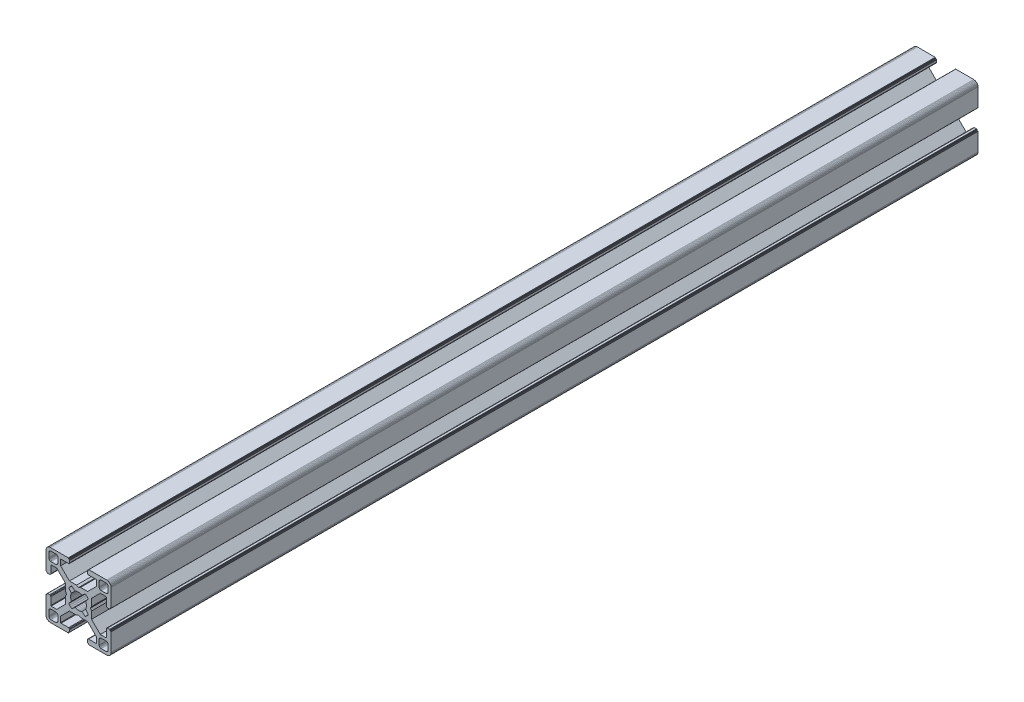
SolidWorks part; units mm, degrees
ref_plane "Front Plane" through (0, 0, 0) normal (0, 0, 1) x (1, 0, 0)
ref_plane "Top Plane" through (0, 0, 0) normal (0, 1, 0) x (1, 0, 0)
ref_plane "Right Plane" through (0, 0, 0) normal (1, 0, 0) x (0, 0, -1)
ref_plane "Plane1" through (0, 0, 0) normal (0, 0, 1) x (1, 0, 0)
sketch "Sketch1" plane through (0, 0, 0) normal (0, 0, 1) x (1, 0, 0)
  line L0 (28.3473, 29.9696) -> (28, 30)
  line L1 (28, 30) -> (19.75, 30)
  line L2 (19.75, 30) -> (19.7153, 29.997)
  line L3 (19.7153, 29.997) -> (19.6816, 29.9879)
  line L4 (19.6816, 29.9879) -> (19.65, 29.9732)
  line L5 (19.65, 29.9732) -> (19.6214, 29.9532)
  line L6 (19.6214, 29.9532) -> (19.5968, 29.9286)
  line L7 (19.5968, 29.9286) -> (19.5768, 29.9)
  line L8 (19.5768, 29.9) -> (19.5621, 29.8684)
  line L9 (19.5621, 29.8684) -> (19.553, 29.8347)
  line L10 (19.553, 29.8347) -> (19.55, 29.8)
  line L11 (19.55, 29.8) -> (19.55, 29.7)
  line L12 (19.55, 29.7) -> (19.547, 29.6653)
  line L13 (19.547, 29.6653) -> (19.5379, 29.6316)
  line L14 (19.5379, 29.6316) -> (19.5232, 29.6)
  line L15 (19.5232, 29.6) -> (19.5032, 29.5714)
  line L16 (19.5032, 29.5714) -> (19.4786, 29.5468)
  line L17 (19.4786, 29.5468) -> (19.45, 29.5268)
  line L18 (19.45, 29.5268) -> (19.4184, 29.5121)
  line L19 (19.4184, 29.5121) -> (19.3847, 29.503)
  line L20 (19.3847, 29.503) -> (19.35, 29.5)
  line L21 (19.35, 29.5) -> (19.25, 29.5)
  line L22 (19.25, 29.5) -> (19.2153, 29.497)
  line L23 (19.2153, 29.497) -> (19.1816, 29.4879)
  line L24 (19.1816, 29.4879) -> (19.15, 29.4732)
  line L25 (19.15, 29.4732) -> (19.1214, 29.4532)
  line L26 (19.1214, 29.4532) -> (19.0968, 29.4286)
  line L27 (19.0968, 29.4286) -> (19.0768, 29.4)
  line L28 (19.0768, 29.4) -> (19.0621, 29.3684)
  line L29 (19.0621, 29.3684) -> (19.053, 29.3347)
  line L30 (19.053, 29.3347) -> (19.05, 29.3)
  line L31 (19.05, 29.3) -> (19.05, 28.4)
  line L32 (19.05, 28.4) -> (19.0591, 28.2958)
  line L33 (19.0591, 28.2958) -> (19.0862, 28.1948)
  line L34 (19.0862, 28.1948) -> (19.1304, 28.1)
  line L35 (19.1304, 28.1) -> (19.1904, 28.0143)
  line L36 (19.1904, 28.0143) -> (19.2643, 27.9404)
  line L37 (19.2643, 27.9404) -> (19.35, 27.8804)
  line L38 (19.35, 27.8804) -> (19.4448, 27.8362)
  line L39 (19.4448, 27.8362) -> (19.5458, 27.8091)
  line L40 (19.5458, 27.8091) -> (19.65, 27.8)
  line L41 (19.65, 27.8) -> (23.05, 27.8)
  line L42 (23.05, 27.8) -> (23.0847, 27.7969)
  line L43 (23.0847, 27.7969) -> (23.1184, 27.7879)
  line L44 (23.1184, 27.7879) -> (23.15, 27.7732)
  line L45 (23.15, 27.7732) -> (23.1786, 27.7532)
  line L46 (23.1786, 27.7532) -> (23.2032, 27.7285)
  line L47 (23.2032, 27.7285) -> (23.2232, 27.7)
  line L48 (23.2232, 27.7) -> (23.2379, 27.6684)
  line L49 (23.2379, 27.6684) -> (23.247, 27.6347)
  line L50 (23.247, 27.6347) -> (23.25, 27.6)
  line L51 (23.25, 27.6) -> (23.25, 25.05)
  line L52 (23.25, 25.05) -> (19.2045, 21)
  line L53 (19.2045, 21) -> (15.9, 21)
  line L54 (15.9, 21) -> (15, 20.4848)
  line L55 (15, 20.4848) -> (14.1, 21)
  line L56 (14.1, 21) -> (10.7955, 21)
  line L57 (10.7955, 21) -> (7.9973, 23.8013)
  line L58 (7.9973, 23.8013) -> (6.75, 25.05)
  line L59 (6.75, 25.05) -> (6.75, 27.6)
  line L60 (6.75, 27.6) -> (6.753, 27.6347)
  line L61 (6.753, 27.6347) -> (6.7621, 27.6684)
  line L62 (6.7621, 27.6684) -> (6.7768, 27.7)
  line L63 (6.7768, 27.7) -> (6.7968, 27.7285)
  line L64 (6.7968, 27.7285) -> (6.8215, 27.7532)
  line L65 (6.8215, 27.7532) -> (6.85, 27.7732)
  line L66 (6.85, 27.7732) -> (6.8816, 27.7879)
  line L67 (6.8816, 27.7879) -> (6.9153, 27.7969)
  line L68 (6.9153, 27.7969) -> (6.95, 27.8)
  line L69 (6.95, 27.8) -> (10.35, 27.8)
  line L70 (10.35, 27.8) -> (10.4542, 27.8091)
  line L71 (10.4542, 27.8091) -> (10.5552, 27.8362)
  line L72 (10.5552, 27.8362) -> (10.65, 27.8804)
  line L73 (10.65, 27.8804) -> (10.7357, 27.9404)
  line L74 (10.7357, 27.9404) -> (10.8096, 28.0143)
  line L75 (10.8096, 28.0143) -> (10.8696, 28.1)
  line L76 (10.8696, 28.1) -> (10.9138, 28.1948)
  line L77 (10.9138, 28.1948) -> (10.9409, 28.2958)
  line L78 (10.9409, 28.2958) -> (10.95, 28.4)
  line L79 (10.95, 28.4) -> (10.95, 29.3)
  line L80 (10.95, 29.3) -> (10.947, 29.3347)
  line L81 (10.947, 29.3347) -> (10.938, 29.3684)
  line L82 (10.938, 29.3684) -> (10.9232, 29.4)
  line L83 (10.9232, 29.4) -> (10.9032, 29.4286)
  line L84 (10.9032, 29.4286) -> (10.8786, 29.4532)
  line L85 (10.8786, 29.4532) -> (10.85, 29.4732)
  line L86 (10.85, 29.4732) -> (10.8184, 29.4879)
  line L87 (10.8184, 29.4879) -> (10.7847, 29.497)
  line L88 (10.7847, 29.497) -> (10.75, 29.5)
  line L89 (10.75, 29.5) -> (10.65, 29.5)
  line L90 (10.65, 29.5) -> (10.6153, 29.503)
  line L91 (10.6153, 29.503) -> (10.5816, 29.5121)
  line L92 (10.5816, 29.5121) -> (10.55, 29.5268)
  line L93 (10.55, 29.5268) -> (10.5214, 29.5468)
  line L94 (10.5214, 29.5468) -> (10.4968, 29.5714)
  line L95 (10.4968, 29.5714) -> (10.4768, 29.6)
  line L96 (10.4768, 29.6) -> (10.4621, 29.6316)
  line L97 (10.4621, 29.6316) -> (10.453, 29.6653)
  line L98 (10.453, 29.6653) -> (10.45, 29.7)
  line L99 (10.45, 29.7) -> (10.45, 29.8)
  line L100 (10.45, 29.8) -> (10.447, 29.8347)
  line L101 (10.447, 29.8347) -> (10.4379, 29.8684)
  line L102 (10.4379, 29.8684) -> (10.4232, 29.9)
  line L103 (10.4232, 29.9) -> (10.4032, 29.9286)
  line L104 (10.4032, 29.9286) -> (10.3786, 29.9532)
  line L105 (10.3786, 29.9532) -> (10.35, 29.9732)
  line L106 (10.35, 29.9732) -> (10.3184, 29.9879)
  line L107 (10.3184, 29.9879) -> (10.2847, 29.997)
  line L108 (10.2847, 29.997) -> (10.25, 30)
  line L109 (10.25, 30) -> (2, 30)
  line L110 (2, 30) -> (1.6527, 29.9696)
  line L111 (1.6527, 29.9696) -> (1.316, 29.8794)
  line L112 (1.316, 29.8794) -> (1, 29.7321)
  line L113 (1, 29.7321) -> (0.7144, 29.5321)
  line L114 (0.7144, 29.5321) -> (0.4679, 29.2856)
  line L115 (0.4679, 29.2856) -> (0.2679, 29)
  line L116 (0.2679, 29) -> (0.1206, 28.684)
  line L117 (0.1206, 28.684) -> (0.0304, 28.3473)
  line L118 (0.0304, 28.3473) -> (0, 28)
  line L119 (0, 28) -> (0, 19.75)
  line L120 (0, 19.75) -> (0.003, 19.7153)
  line L121 (0.003, 19.7153) -> (0.0121, 19.6816)
  line L122 (0.0121, 19.6816) -> (0.0268, 19.65)
  line L123 (0.0268, 19.65) -> (0.0468, 19.6214)
  line L124 (0.0468, 19.6214) -> (0.0714, 19.5968)
  line L125 (0.0714, 19.5968) -> (0.1, 19.5768)
  line L126 (0.1, 19.5768) -> (0.1316, 19.5621)
  line L127 (0.1316, 19.5621) -> (0.1653, 19.553)
  line L128 (0.1653, 19.553) -> (0.2, 19.55)
  line L129 (0.2, 19.55) -> (0.3, 19.55)
  line L130 (0.3, 19.55) -> (0.3347, 19.547)
  line L131 (0.3347, 19.547) -> (0.3684, 19.5379)
  line L132 (0.3684, 19.5379) -> (0.4, 19.5232)
  line L133 (0.4, 19.5232) -> (0.4286, 19.5032)
  line L134 (0.4286, 19.5032) -> (0.4532, 19.4786)
  line L135 (0.4532, 19.4786) -> (0.4732, 19.45)
  line L136 (0.4732, 19.45) -> (0.4879, 19.4184)
  line L137 (0.4879, 19.4184) -> (0.497, 19.3847)
  line L138 (0.497, 19.3847) -> (0.5, 19.35)
  line L139 (0.5, 19.35) -> (0.5, 19.25)
  line L140 (0.5, 19.25) -> (0.503, 19.2153)
  line L141 (0.503, 19.2153) -> (0.5121, 19.1816)
  line L142 (0.5121, 19.1816) -> (0.5268, 19.15)
  line L143 (0.5268, 19.15) -> (0.5468, 19.1214)
  line L144 (0.5468, 19.1214) -> (0.5714, 19.0968)
  line L145 (0.5714, 19.0968) -> (0.6, 19.0768)
  line L146 (0.6, 19.0768) -> (0.6316, 19.0621)
  line L147 (0.6316, 19.0621) -> (0.6653, 19.053)
  line L148 (0.6653, 19.053) -> (0.7, 19.05)
  line L149 (0.7, 19.05) -> (1.6, 19.05)
  line L150 (1.6, 19.05) -> (1.7042, 19.0591)
  line L151 (1.7042, 19.0591) -> (1.8052, 19.0862)
  line L152 (1.8052, 19.0862) -> (1.9, 19.1304)
  line L153 (1.9, 19.1304) -> (1.9857, 19.1904)
  line L154 (1.9857, 19.1904) -> (2.0596, 19.2643)
  line L155 (2.0596, 19.2643) -> (2.1196, 19.35)
  line L156 (2.1196, 19.35) -> (2.1638, 19.4448)
  line L157 (2.1638, 19.4448) -> (2.1909, 19.5458)
  line L158 (2.1909, 19.5458) -> (2.2, 19.65)
  line L159 (2.2, 19.65) -> (2.2, 23.05)
  line L160 (2.2, 23.05) -> (2.203, 23.0847)
  line L161 (2.203, 23.0847) -> (2.2121, 23.1184)
  line L162 (2.2121, 23.1184) -> (2.2268, 23.15)
  line L163 (2.2268, 23.15) -> (2.2468, 23.1786)
  line L164 (2.2468, 23.1786) -> (2.2714, 23.2032)
  line L165 (2.2714, 23.2032) -> (2.3, 23.2232)
  line L166 (2.3, 23.2232) -> (2.3316, 23.2379)
  line L167 (2.3316, 23.2379) -> (2.3653, 23.247)
  line L168 (2.3653, 23.247) -> (2.4, 23.25)
  line L169 (2.4, 23.25) -> (4.95, 23.25)
  line L170 (4.95, 23.25) -> (7.9973, 20.2027)
  line L171 (7.9973, 20.2027) -> (8.9955, 19.2045)
  line L172 (8.9955, 19.2045) -> (8.9955, 15.9)
  line L173 (8.9955, 15.9) -> (9.5151, 15)
  line L174 (9.5151, 15) -> (8.9955, 14.1)
  line L175 (8.9955, 14.1) -> (8.9955, 10.7955)
  line L176 (8.9955, 10.7955) -> (4.95, 6.75)
  line L177 (4.95, 6.75) -> (2.4, 6.75)
  line L178 (2.4, 6.75) -> (2.3653, 6.753)
  line L179 (2.3653, 6.753) -> (2.3316, 6.7621)
  line L180 (2.3316, 6.7621) -> (2.3, 6.7768)
  line L181 (2.3, 6.7768) -> (2.2714, 6.7968)
  line L182 (2.2714, 6.7968) -> (2.2468, 6.8214)
  line L183 (2.2468, 6.8214) -> (2.2268, 6.85)
  line L184 (2.2268, 6.85) -> (2.2121, 6.8816)
  line L185 (2.2121, 6.8816) -> (2.203, 6.9153)
  line L186 (2.203, 6.9153) -> (2.2, 6.95)
  line L187 (2.2, 6.95) -> (2.2, 10.35)
  line L188 (2.2, 10.35) -> (2.1909, 10.4542)
  line L189 (2.1909, 10.4542) -> (2.1638, 10.5552)
  line L190 (2.1638, 10.5552) -> (2.1196, 10.65)
  line L191 (2.1196, 10.65) -> (2.0596, 10.7357)
  line L192 (2.0596, 10.7357) -> (1.9857, 10.8096)
  line L193 (1.9857, 10.8096) -> (1.9, 10.8696)
  line L194 (1.9, 10.8696) -> (1.8052, 10.9138)
  line L195 (1.8052, 10.9138) -> (1.7042, 10.9409)
  line L196 (1.7042, 10.9409) -> (1.6, 10.95)
  line L197 (1.6, 10.95) -> (0.7, 10.95)
  line L198 (0.7, 10.95) -> (0.6653, 10.9469)
  line L199 (0.6653, 10.9469) -> (0.6316, 10.9379)
  line L200 (0.6316, 10.9379) -> (0.6, 10.9232)
  line L201 (0.6, 10.9232) -> (0.5715, 10.9032)
  line L202 (0.5715, 10.9032) -> (0.5468, 10.8785)
  line L203 (0.5468, 10.8785) -> (0.5268, 10.85)
  line L204 (0.5268, 10.85) -> (0.5121, 10.8184)
  line L205 (0.5121, 10.8184) -> (0.503, 10.7847)
  line L206 (0.503, 10.7847) -> (0.5, 10.75)
  line L207 (0.5, 10.75) -> (0.5, 10.65)
  line L208 (0.5, 10.65) -> (0.497, 10.6153)
  line L209 (0.497, 10.6153) -> (0.4879, 10.5816)
  line L210 (0.4879, 10.5816) -> (0.4732, 10.55)
  line L211 (0.4732, 10.55) -> (0.4532, 10.5214)
  line L212 (0.4532, 10.5214) -> (0.4286, 10.4968)
  line L213 (0.4286, 10.4968) -> (0.4, 10.4768)
  line L214 (0.4, 10.4768) -> (0.3684, 10.4621)
  line L215 (0.3684, 10.4621) -> (0.3347, 10.453)
  line L216 (0.3347, 10.453) -> (0.3, 10.45)
  line L217 (0.3, 10.45) -> (0.2, 10.45)
  line L218 (0.2, 10.45) -> (0.1653, 10.447)
  line L219 (0.1653, 10.447) -> (0.1316, 10.4379)
  line L220 (0.1316, 10.4379) -> (0.1, 10.4232)
  line L221 (0.1, 10.4232) -> (0.0714, 10.4032)
  line L222 (0.0714, 10.4032) -> (0.0468, 10.3786)
  line L223 (0.0468, 10.3786) -> (0.0268, 10.35)
  line L224 (0.0268, 10.35) -> (0.0121, 10.3184)
  line L225 (0.0121, 10.3184) -> (0.003, 10.2847)
  line L226 (0.003, 10.2847) -> (0, 10.25)
  line L227 (0, 10.25) -> (0, 2)
  line L228 (0, 2) -> (0.0304, 1.6527)
  line L229 (0.0304, 1.6527) -> (0.1206, 1.316)
  line L230 (0.1206, 1.316) -> (0.2679, 1)
  line L231 (0.2679, 1) -> (0.4679, 0.7144)
  line L232 (0.4679, 0.7144) -> (0.7144, 0.4679)
  line L233 (0.7144, 0.4679) -> (1, 0.2679)
  line L234 (1, 0.2679) -> (1.316, 0.1206)
  line L235 (1.316, 0.1206) -> (1.6527, 0.0304)
  line L236 (1.6527, 0.0304) -> (2, 0)
  line L237 (2, 0) -> (10.25, 0)
  line L238 (10.25, 0) -> (10.2847, 0.003)
  line L239 (10.2847, 0.003) -> (10.3184, 0.0121)
  line L240 (10.3184, 0.0121) -> (10.35, 0.0268)
  line L241 (10.35, 0.0268) -> (10.3786, 0.0468)
  line L242 (10.3786, 0.0468) -> (10.4032, 0.0714)
  line L243 (10.4032, 0.0714) -> (10.4232, 0.1)
  line L244 (10.4232, 0.1) -> (10.4379, 0.1316)
  line L245 (10.4379, 0.1316) -> (10.447, 0.1653)
  line L246 (10.447, 0.1653) -> (10.45, 0.2)
  line L247 (10.45, 0.2) -> (10.45, 0.3)
  line L248 (10.45, 0.3) -> (10.453, 0.3347)
  line L249 (10.453, 0.3347) -> (10.4621, 0.3684)
  line L250 (10.4621, 0.3684) -> (10.4768, 0.4)
  line L251 (10.4768, 0.4) -> (10.4968, 0.4286)
  line L252 (10.4968, 0.4286) -> (10.5214, 0.4532)
  line L253 (10.5214, 0.4532) -> (10.55, 0.4732)
  line L254 (10.55, 0.4732) -> (10.5816, 0.4879)
  line L255 (10.5816, 0.4879) -> (10.6153, 0.497)
  line L256 (10.6153, 0.497) -> (10.65, 0.5)
  line L257 (10.65, 0.5) -> (10.75, 0.5)
  line L258 (10.75, 0.5) -> (10.7847, 0.503)
  line L259 (10.7847, 0.503) -> (10.8184, 0.5121)
  line L260 (10.8184, 0.5121) -> (10.85, 0.5268)
  line L261 (10.85, 0.5268) -> (10.8785, 0.5468)
  line L262 (10.8785, 0.5468) -> (10.9032, 0.5715)
  line L263 (10.9032, 0.5715) -> (10.9232, 0.6)
  line L264 (10.9232, 0.6) -> (10.9379, 0.6316)
  line L265 (10.9379, 0.6316) -> (10.9469, 0.6653)
  line L266 (10.9469, 0.6653) -> (10.95, 0.7)
  line L267 (10.95, 0.7) -> (10.95, 1.6)
  line L268 (10.95, 1.6) -> (10.9409, 1.7042)
  line L269 (10.9409, 1.7042) -> (10.9138, 1.8052)
  line L270 (10.9138, 1.8052) -> (10.8696, 1.9)
  line L271 (10.8696, 1.9) -> (10.8096, 1.9857)
  line L272 (10.8096, 1.9857) -> (10.7357, 2.0596)
  line L273 (10.7357, 2.0596) -> (10.65, 2.1196)
  line L274 (10.65, 2.1196) -> (10.5552, 2.1638)
  line L275 (10.5552, 2.1638) -> (10.4542, 2.1909)
  line L276 (10.4542, 2.1909) -> (10.35, 2.2)
  line L277 (10.35, 2.2) -> (6.95, 2.2)
  line L278 (6.95, 2.2) -> (6.9153, 2.203)
  line L279 (6.9153, 2.203) -> (6.8816, 2.212)
  line L280 (6.8816, 2.212) -> (6.85, 2.2268)
  line L281 (6.85, 2.2268) -> (6.8215, 2.2468)
  line L282 (6.8215, 2.2468) -> (6.7968, 2.2714)
  line L283 (6.7968, 2.2714) -> (6.7768, 2.3)
  line L284 (6.7768, 2.3) -> (6.7621, 2.3316)
  line L285 (6.7621, 2.3316) -> (6.753, 2.3653)
  line L286 (6.753, 2.3653) -> (6.75, 2.4)
  line L287 (6.75, 2.4) -> (6.75, 4.95)
  line L288 (6.75, 4.95) -> (9.7875, 7.9908)
  line L289 (9.7875, 7.9908) -> (10.7955, 9)
  line L290 (10.7955, 9) -> (14.1, 9)
  line L291 (14.1, 9) -> (15, 9.5151)
  line L292 (15, 9.5151) -> (15.9, 9)
  line L293 (15.9, 9) -> (19.2045, 9)
  line L294 (19.2045, 9) -> (20.2126, 7.9908)
  line L295 (20.2126, 7.9908) -> (23.25, 4.95)
  line L296 (23.25, 4.95) -> (23.25, 2.4)
  line L297 (23.25, 2.4) -> (23.247, 2.3653)
  line L298 (23.247, 2.3653) -> (23.2379, 2.3316)
  line L299 (23.2379, 2.3316) -> (23.2232, 2.3)
  line L300 (23.2232, 2.3) -> (23.2032, 2.2714)
  line L301 (23.2032, 2.2714) -> (23.1786, 2.2468)
  line L302 (23.1786, 2.2468) -> (23.15, 2.2268)
  line L303 (23.15, 2.2268) -> (23.1184, 2.212)
  line L304 (23.1184, 2.212) -> (23.0847, 2.203)
  line L305 (23.0847, 2.203) -> (23.05, 2.2)
  line L306 (23.05, 2.2) -> (19.65, 2.2)
  line L307 (19.65, 2.2) -> (19.5458, 2.1909)
  line L308 (19.5458, 2.1909) -> (19.4448, 2.1638)
  line L309 (19.4448, 2.1638) -> (19.35, 2.1196)
  line L310 (19.35, 2.1196) -> (19.2643, 2.0596)
  line L311 (19.2643, 2.0596) -> (19.1904, 1.9857)
  line L312 (19.1904, 1.9857) -> (19.1304, 1.9)
  line L313 (19.1304, 1.9) -> (19.0862, 1.8052)
  line L314 (19.0862, 1.8052) -> (19.0591, 1.7042)
  line L315 (19.0591, 1.7042) -> (19.05, 1.6)
  line L316 (19.05, 1.6) -> (19.05, 0.7)
  line L317 (19.05, 0.7) -> (19.053, 0.6653)
  line L318 (19.053, 0.6653) -> (19.0621, 0.6316)
  line L319 (19.0621, 0.6316) -> (19.0768, 0.6)
  line L320 (19.0768, 0.6) -> (19.0968, 0.5714)
  line L321 (19.0968, 0.5714) -> (19.1214, 0.5468)
  line L322 (19.1214, 0.5468) -> (19.15, 0.5268)
  line L323 (19.15, 0.5268) -> (19.1816, 0.5121)
  line L324 (19.1816, 0.5121) -> (19.2153, 0.503)
  line L325 (19.2153, 0.503) -> (19.25, 0.5)
  line L326 (19.25, 0.5) -> (19.35, 0.5)
  line L327 (19.35, 0.5) -> (19.3847, 0.497)
  line L328 (19.3847, 0.497) -> (19.4184, 0.4879)
  line L329 (19.4184, 0.4879) -> (19.45, 0.4732)
  line L330 (19.45, 0.4732) -> (19.4786, 0.4532)
  line L331 (19.4786, 0.4532) -> (19.5032, 0.4286)
  line L332 (19.5032, 0.4286) -> (19.5232, 0.4)
  line L333 (19.5232, 0.4) -> (19.5379, 0.3684)
  line L334 (19.5379, 0.3684) -> (19.547, 0.3347)
  line L335 (19.547, 0.3347) -> (19.55, 0.3)
  line L336 (19.55, 0.3) -> (19.55, 0.2)
  line L337 (19.55, 0.2) -> (19.553, 0.1653)
  line L338 (19.553, 0.1653) -> (19.5621, 0.1316)
  line L339 (19.5621, 0.1316) -> (19.5768, 0.1)
  line L340 (19.5768, 0.1) -> (19.5968, 0.0714)
  line L341 (19.5968, 0.0714) -> (19.6214, 0.0468)
  line L342 (19.6214, 0.0468) -> (19.65, 0.0268)
  line L343 (19.65, 0.0268) -> (19.6816, 0.0121)
  line L344 (19.6816, 0.0121) -> (19.7153, 0.003)
  line L345 (19.7153, 0.003) -> (19.75, 0)
  line L346 (19.75, 0) -> (28, 0)
  line L347 (28, 0) -> (28.3473, 0.0304)
  line L348 (28.3473, 0.0304) -> (28.684, 0.1206)
  line L349 (28.684, 0.1206) -> (29, 0.2679)
  line L350 (29, 0.2679) -> (29.2856, 0.4679)
  line L351 (29.2856, 0.4679) -> (29.5321, 0.7144)
  line L352 (29.5321, 0.7144) -> (29.7321, 1)
  line L353 (29.7321, 1) -> (29.8794, 1.316)
  line L354 (29.8794, 1.316) -> (29.9696, 1.6527)
  line L355 (29.9696, 1.6527) -> (30, 2)
  line L356 (30, 2) -> (30, 10.25)
  line L357 (30, 10.25) -> (29.997, 10.2847)
  line L358 (29.997, 10.2847) -> (29.988, 10.3184)
  line L359 (29.988, 10.3184) -> (29.9732, 10.35)
  line L360 (29.9732, 10.35) -> (29.9532, 10.3785)
  line L361 (29.9532, 10.3785) -> (29.9286, 10.4032)
  line L362 (29.9286, 10.4032) -> (29.9, 10.4232)
  line L363 (29.9, 10.4232) -> (29.8684, 10.4379)
  line L364 (29.8684, 10.4379) -> (29.8347, 10.447)
  line L365 (29.8347, 10.447) -> (29.8, 10.45)
  line L366 (29.8, 10.45) -> (29.7, 10.45)
  line L367 (29.7, 10.45) -> (29.6649, 10.4534)
  line L368 (29.6649, 10.4534) -> (29.6312, 10.4624)
  line L369 (29.6312, 10.4624) -> (29.5996, 10.4772)
  line L370 (29.5996, 10.4772) -> (29.5711, 10.4972)
  line L371 (29.5711, 10.4972) -> (29.5464, 10.5218)
  line L372 (29.5464, 10.5218) -> (29.5264, 10.5504)
  line L373 (29.5264, 10.5504) -> (29.5117, 10.582)
  line L374 (29.5117, 10.582) -> (29.5027, 10.6156)
  line L375 (29.5027, 10.6156) -> (29.4996, 10.6504)
  line L376 (29.4996, 10.6504) -> (29.4996, 10.7504)
  line L377 (29.4996, 10.7504) -> (29.497, 10.7847)
  line L378 (29.497, 10.7847) -> (29.4879, 10.8184)
  line L379 (29.4879, 10.8184) -> (29.4732, 10.85)
  line L380 (29.4732, 10.85) -> (29.4532, 10.8785)
  line L381 (29.4532, 10.8785) -> (29.4286, 10.9032)
  line L382 (29.4286, 10.9032) -> (29.4, 10.9232)
  line L383 (29.4, 10.9232) -> (29.3684, 10.9379)
  line L384 (29.3684, 10.9379) -> (29.3347, 10.9469)
  line L385 (29.3347, 10.9469) -> (29.3, 10.95)
  line L386 (29.3, 10.95) -> (28.4, 10.95)
  line L387 (28.4, 10.95) -> (28.2958, 10.9409)
  line L388 (28.2958, 10.9409) -> (28.1948, 10.9138)
  line L389 (28.1948, 10.9138) -> (28.1, 10.8696)
  line L390 (28.1, 10.8696) -> (28.0143, 10.8096)
  line L391 (28.0143, 10.8096) -> (27.9404, 10.7357)
  line L392 (27.9404, 10.7357) -> (27.8804, 10.65)
  line L393 (27.8804, 10.65) -> (27.8362, 10.5552)
  line L394 (27.8362, 10.5552) -> (27.8091, 10.4542)
  line L395 (27.8091, 10.4542) -> (27.8, 10.35)
  line L396 (27.8, 10.35) -> (27.8, 6.95)
  line L397 (27.8, 6.95) -> (27.797, 6.9153)
  line L398 (27.797, 6.9153) -> (27.7879, 6.8816)
  line L399 (27.7879, 6.8816) -> (27.7732, 6.85)
  line L400 (27.7732, 6.85) -> (27.7532, 6.8214)
  line L401 (27.7532, 6.8214) -> (27.7286, 6.7968)
  line L402 (27.7286, 6.7968) -> (27.7, 6.7768)
  line L403 (27.7, 6.7768) -> (27.6684, 6.7621)
  line L404 (27.6684, 6.7621) -> (27.6347, 6.753)
  line L405 (27.6347, 6.753) -> (27.6, 6.75)
  line L406 (27.6, 6.75) -> (25.05, 6.75)
  line L407 (25.05, 6.75) -> (23.8092, 7.9908)
  line L408 (23.8092, 7.9908) -> (21.0045, 10.7955)
  line L409 (21.0045, 10.7955) -> (21.0045, 14.1)
  line L410 (21.0045, 14.1) -> (20.4849, 15)
  line L411 (20.4849, 15) -> (21.0045, 15.9)
  line L412 (21.0045, 15.9) -> (21.0045, 19.2045)
  line L413 (21.0045, 19.2045) -> (25.05, 23.25)
  line L414 (25.05, 23.25) -> (27.6, 23.25)
  line L415 (27.6, 23.25) -> (27.6347, 23.247)
  line L416 (27.6347, 23.247) -> (27.6684, 23.2379)
  line L417 (27.6684, 23.2379) -> (27.7, 23.2232)
  line L418 (27.7, 23.2232) -> (27.7286, 23.2032)
  line L419 (27.7286, 23.2032) -> (27.7532, 23.1786)
  line L420 (27.7532, 23.1786) -> (27.7732, 23.15)
  line L421 (27.7732, 23.15) -> (27.7879, 23.1184)
  line L422 (27.7879, 23.1184) -> (27.797, 23.0847)
  line L423 (27.797, 23.0847) -> (27.8, 23.05)
  line L424 (27.8, 23.05) -> (27.8, 19.65)
  line L425 (27.8, 19.65) -> (27.8091, 19.5458)
  line L426 (27.8091, 19.5458) -> (27.8362, 19.4448)
  line L427 (27.8362, 19.4448) -> (27.8804, 19.35)
  line L428 (27.8804, 19.35) -> (27.9404, 19.2643)
  line L429 (27.9404, 19.2643) -> (28.0143, 19.1904)
  line L430 (28.0143, 19.1904) -> (28.1, 19.1304)
  line L431 (28.1, 19.1304) -> (28.1948, 19.0862)
  line L432 (28.1948, 19.0862) -> (28.2958, 19.0591)
  line L433 (28.2958, 19.0591) -> (28.4, 19.05)
  line L434 (28.4, 19.05) -> (29.3, 19.05)
  line L435 (29.3, 19.05) -> (29.3347, 19.053)
  line L436 (29.3347, 19.053) -> (29.3684, 19.0621)
  line L437 (29.3684, 19.0621) -> (29.4, 19.0768)
  line L438 (29.4, 19.0768) -> (29.4282, 19.0971)
  line L439 (29.4282, 19.0971) -> (29.4528, 19.1218)
  line L440 (29.4528, 19.1218) -> (29.4728, 19.1504)
  line L441 (29.4728, 19.1504) -> (29.4876, 19.182)
  line L442 (29.4876, 19.182) -> (29.4966, 19.2156)
  line L443 (29.4966, 19.2156) -> (29.4996, 19.2504)
  line L444 (29.4996, 19.2504) -> (29.4996, 19.3504)
  line L445 (29.4996, 19.3504) -> (29.5027, 19.3851)
  line L446 (29.5027, 19.3851) -> (29.5117, 19.4188)
  line L447 (29.5117, 19.4188) -> (29.5264, 19.4504)
  line L448 (29.5264, 19.4504) -> (29.5464, 19.4789)
  line L449 (29.5464, 19.4789) -> (29.5711, 19.5036)
  line L450 (29.5711, 19.5036) -> (29.5996, 19.5236)
  line L451 (29.5996, 19.5236) -> (29.6312, 19.5383)
  line L452 (29.6312, 19.5383) -> (29.6649, 19.5473)
  line L453 (29.6649, 19.5473) -> (29.7, 19.55)
  line L454 (29.7, 19.55) -> (29.8, 19.55)
  line L455 (29.8, 19.55) -> (29.8347, 19.553)
  line L456 (29.8347, 19.553) -> (29.8684, 19.5621)
  line L457 (29.8684, 19.5621) -> (29.9, 19.5768)
  line L458 (29.9, 19.5768) -> (29.9286, 19.5968)
  line L459 (29.9286, 19.5968) -> (29.9532, 19.6214)
  line L460 (29.9532, 19.6214) -> (29.9732, 19.65)
  line L461 (29.9732, 19.65) -> (29.9879, 19.6816)
  line L462 (29.9879, 19.6816) -> (29.997, 19.7153)
  line L463 (29.997, 19.7153) -> (30, 19.75)
  line L464 (30, 19.75) -> (30, 28)
  line L465 (30, 28) -> (29.9696, 28.3473)
  line L466 (29.9696, 28.3473) -> (29.8794, 28.684)
  line L467 (29.8794, 28.684) -> (29.7321, 29)
  line L468 (29.7321, 29) -> (29.5321, 29.2856)
  line L469 (29.5321, 29.2856) -> (29.2856, 29.5321)
  line L470 (29.2856, 29.5321) -> (29, 29.7321)
  line L471 (29, 29.7321) -> (28.684, 29.8794)
  line L472 (28.684, 29.8794) -> (28.3473, 29.9696)
  line L473 (1.3, 25.5) -> (1.3, 27.7)
  line L474 (1.3, 27.7) -> (1.3123, 27.8564)
  line L475 (1.3123, 27.8564) -> (1.3489, 28.009)
  line L476 (1.3489, 28.009) -> (1.409, 28.154)
  line L477 (1.409, 28.154) -> (1.491, 28.2878)
  line L478 (1.491, 28.2878) -> (1.5929, 28.4071)
  line L479 (1.5929, 28.4071) -> (1.7122, 28.509)
  line L480 (1.7122, 28.509) -> (1.846, 28.591)
  line L481 (1.846, 28.591) -> (1.991, 28.6511)
  line L482 (1.991, 28.6511) -> (2.1436, 28.6877)
  line L483 (2.1436, 28.6877) -> (2.3, 28.7)
  line L484 (2.3, 28.7) -> (4.5, 28.7)
  line L485 (4.5, 28.7) -> (4.6564, 28.6877)
  line L486 (4.6564, 28.6877) -> (4.809, 28.6511)
  line L487 (4.809, 28.6511) -> (4.954, 28.591)
  line L488 (4.954, 28.591) -> (5.0878, 28.509)
  line L489 (5.0878, 28.509) -> (5.2071, 28.4071)
  line L490 (5.2071, 28.4071) -> (5.309, 28.2878)
  line L491 (5.309, 28.2878) -> (5.391, 28.154)
  line L492 (5.391, 28.154) -> (5.4511, 28.009)
  line L493 (5.4511, 28.009) -> (5.4877, 27.8564)
  line L494 (5.4877, 27.8564) -> (5.5, 27.7)
  line L495 (5.5, 27.7) -> (5.5, 25.5)
  line L496 (5.5, 25.5) -> (5.4877, 25.3436)
  line L497 (5.4877, 25.3436) -> (5.4511, 25.191)
  line L498 (5.4511, 25.191) -> (5.391, 25.046)
  line L499 (5.391, 25.046) -> (5.309, 24.9122)
  line L500 (5.309, 24.9122) -> (5.2071, 24.7929)
  line L501 (5.2071, 24.7929) -> (5.0878, 24.691)
  line L502 (5.0878, 24.691) -> (4.954, 24.609)
  line L503 (4.954, 24.609) -> (4.809, 24.5489)
  line L504 (4.809, 24.5489) -> (4.6564, 24.5123)
  line L505 (4.6564, 24.5123) -> (4.5, 24.5)
  line L506 (4.5, 24.5) -> (2.3, 24.5)
  line L507 (2.3, 24.5) -> (2.1436, 24.5123)
  line L508 (2.1436, 24.5123) -> (1.991, 24.5489)
  line L509 (1.991, 24.5489) -> (1.846, 24.609)
  line L510 (1.846, 24.609) -> (1.7122, 24.691)
  line L511 (1.7122, 24.691) -> (1.5929, 24.7929)
  line L512 (1.5929, 24.7929) -> (1.491, 24.9122)
  line L513 (1.491, 24.9122) -> (1.409, 25.046)
  line L514 (1.409, 25.046) -> (1.3489, 25.191)
  line L515 (1.3489, 25.191) -> (1.3123, 25.3436)
  line L516 (1.3123, 25.3436) -> (1.3, 25.5)
  line L517 (25.3436, 28.6877) -> (25.5, 28.7)
  line L518 (25.5, 28.7) -> (27.7, 28.7)
  line L519 (27.7, 28.7) -> (27.8564, 28.6877)
  line L520 (27.8564, 28.6877) -> (28.009, 28.6511)
  line L521 (28.009, 28.6511) -> (28.154, 28.591)
  line L522 (28.154, 28.591) -> (28.2878, 28.509)
  line L523 (28.2878, 28.509) -> (28.4071, 28.4071)
  line L524 (28.4071, 28.4071) -> (28.509, 28.2878)
  line L525 (28.509, 28.2878) -> (28.591, 28.154)
  line L526 (28.591, 28.154) -> (28.6511, 28.009)
  line L527 (28.6511, 28.009) -> (28.6877, 27.8564)
  line L528 (28.6877, 27.8564) -> (28.7, 27.7)
  line L529 (28.7, 27.7) -> (28.7, 25.5)
  line L530 (28.7, 25.5) -> (28.6877, 25.3436)
  line L531 (28.6877, 25.3436) -> (28.6511, 25.191)
  line L532 (28.6511, 25.191) -> (28.591, 25.046)
  line L533 (28.591, 25.046) -> (28.509, 24.9122)
  line L534 (28.509, 24.9122) -> (28.4071, 24.7929)
  line L535 (28.4071, 24.7929) -> (28.2878, 24.691)
  line L536 (28.2878, 24.691) -> (28.154, 24.609)
  line L537 (28.154, 24.609) -> (28.009, 24.5489)
  line L538 (28.009, 24.5489) -> (27.8564, 24.5123)
  line L539 (27.8564, 24.5123) -> (27.7, 24.5)
  line L540 (27.7, 24.5) -> (25.5, 24.5)
  line L541 (25.5, 24.5) -> (25.3436, 24.5123)
  line L542 (25.3436, 24.5123) -> (25.191, 24.5489)
  line L543 (25.191, 24.5489) -> (25.046, 24.609)
  line L544 (25.046, 24.609) -> (24.9122, 24.691)
  line L545 (24.9122, 24.691) -> (24.7929, 24.7929)
  line L546 (24.7929, 24.7929) -> (24.691, 24.9122)
  line L547 (24.691, 24.9122) -> (24.609, 25.046)
  line L548 (24.609, 25.046) -> (24.5489, 25.191)
  line L549 (24.5489, 25.191) -> (24.5123, 25.3436)
  line L550 (24.5123, 25.3436) -> (24.5, 25.5)
  line L551 (24.5, 25.5) -> (24.5, 27.7)
  line L552 (24.5, 27.7) -> (24.5123, 27.8564)
  line L553 (24.5123, 27.8564) -> (24.5489, 28.009)
  line L554 (24.5489, 28.009) -> (24.609, 28.154)
  line L555 (24.609, 28.154) -> (24.691, 28.2878)
  line L556 (24.691, 28.2878) -> (24.7929, 28.4071)
  line L557 (24.7929, 28.4071) -> (24.9122, 28.509)
  line L558 (24.9122, 28.509) -> (25.046, 28.591)
  line L559 (25.046, 28.591) -> (25.191, 28.6511)
  line L560 (25.191, 28.6511) -> (25.3436, 28.6877)
  line L561 (15, 18.65) -> (15.55, 18.6083)
  line L562 (15.55, 18.6083) -> (16.0875, 18.4842)
  line L563 (16.0875, 18.4842) -> (16.6001, 18.2806)
  line L564 (16.6001, 18.2806) -> (18.1359, 19.5184)
  line L565 (18.1359, 19.5184) -> (18.645, 19.1187)
  line L566 (18.645, 19.1187) -> (19.1036, 18.6621)
  line L567 (19.1036, 18.6621) -> (19.5053, 18.1547)
  line L568 (19.5053, 18.1547) -> (18.2806, 16.6001)
  line L569 (18.2806, 16.6001) -> (18.4842, 16.0875)
  line L570 (18.4842, 16.0875) -> (18.6083, 15.55)
  line L571 (18.6083, 15.55) -> (18.65, 15)
  line L572 (18.65, 15) -> (18.6083, 14.45)
  line L573 (18.6083, 14.45) -> (18.4842, 13.9125)
  line L574 (18.4842, 13.9125) -> (18.2806, 13.3999)
  line L575 (18.2806, 13.3999) -> (19.5053, 11.8453)
  line L576 (19.5053, 11.8453) -> (19.1036, 11.3379)
  line L577 (19.1036, 11.3379) -> (18.645, 10.8813)
  line L578 (18.645, 10.8813) -> (18.1359, 10.4816)
  line L579 (18.1359, 10.4816) -> (16.6001, 11.7194)
  line L580 (16.6001, 11.7194) -> (16.0875, 11.5158)
  line L581 (16.0875, 11.5158) -> (15.55, 11.3917)
  line L582 (15.55, 11.3917) -> (15, 11.35)
  line L583 (15, 11.35) -> (14.45, 11.3917)
  line L584 (14.45, 11.3917) -> (13.9125, 11.5158)
  line L585 (13.9125, 11.5158) -> (13.3999, 11.7194)
  line L586 (13.3999, 11.7194) -> (11.8641, 10.4816)
  line L587 (11.8641, 10.4816) -> (11.355, 10.8813)
  line L588 (11.355, 10.8813) -> (10.8964, 11.3379)
  line L589 (10.8964, 11.3379) -> (10.4947, 11.8453)
  line L590 (10.4947, 11.8453) -> (11.7194, 13.3999)
  line L591 (11.7194, 13.3999) -> (11.5158, 13.9125)
  line L592 (11.5158, 13.9125) -> (11.3917, 14.45)
  line L593 (11.3917, 14.45) -> (11.35, 15)
  line L594 (11.35, 15) -> (11.3917, 15.55)
  line L595 (11.3917, 15.55) -> (11.5158, 16.0875)
  line L596 (11.5158, 16.0875) -> (11.7194, 16.6001)
  line L597 (11.7194, 16.6001) -> (10.4947, 18.1547)
  line L598 (10.4947, 18.1547) -> (10.8964, 18.6621)
  line L599 (10.8964, 18.6621) -> (11.355, 19.1187)
  line L600 (11.355, 19.1187) -> (11.8641, 19.5184)
  line L601 (11.8641, 19.5184) -> (13.3999, 18.2806)
  line L602 (13.3999, 18.2806) -> (13.9125, 18.4842)
  line L603 (13.9125, 18.4842) -> (14.45, 18.6083)
  line L604 (14.45, 18.6083) -> (15, 18.65)
  line L605 (4.5, 1.3) -> (2.3, 1.3)
  line L606 (2.3, 1.3) -> (2.1436, 1.3123)
  line L607 (2.1436, 1.3123) -> (1.991, 1.3489)
  line L608 (1.991, 1.3489) -> (1.846, 1.409)
  line L609 (1.846, 1.409) -> (1.7122, 1.491)
  line L610 (1.7122, 1.491) -> (1.5929, 1.5929)
  line L611 (1.5929, 1.5929) -> (1.491, 1.7122)
  line L612 (1.491, 1.7122) -> (1.409, 1.846)
  line L613 (1.409, 1.846) -> (1.3489, 1.991)
  line L614 (1.3489, 1.991) -> (1.3123, 2.1436)
  line L615 (1.3123, 2.1436) -> (1.3, 2.3)
  line L616 (1.3, 2.3) -> (1.3, 4.5)
  line L617 (1.3, 4.5) -> (1.3123, 4.6564)
  line L618 (1.3123, 4.6564) -> (1.3489, 4.809)
  line L619 (1.3489, 4.809) -> (1.409, 4.954)
  line L620 (1.409, 4.954) -> (1.491, 5.0878)
  line L621 (1.491, 5.0878) -> (1.5929, 5.2071)
  line L622 (1.5929, 5.2071) -> (1.7122, 5.309)
  line L623 (1.7122, 5.309) -> (1.846, 5.391)
  line L624 (1.846, 5.391) -> (1.991, 5.4511)
  line L625 (1.991, 5.4511) -> (2.1436, 5.4877)
  line L626 (2.1436, 5.4877) -> (2.3, 5.5)
  line L627 (2.3, 5.5) -> (4.5, 5.5)
  line L628 (4.5, 5.5) -> (4.6564, 5.4877)
  line L629 (4.6564, 5.4877) -> (4.809, 5.4511)
  line L630 (4.809, 5.4511) -> (4.954, 5.391)
  line L631 (4.954, 5.391) -> (5.0878, 5.309)
  line L632 (5.0878, 5.309) -> (5.2071, 5.2071)
  line L633 (5.2071, 5.2071) -> (5.309, 5.0878)
  line L634 (5.309, 5.0878) -> (5.391, 4.954)
  line L635 (5.391, 4.954) -> (5.4511, 4.809)
  line L636 (5.4511, 4.809) -> (5.4877, 4.6564)
  line L637 (5.4877, 4.6564) -> (5.5, 4.5)
  line L638 (5.5, 4.5) -> (5.5, 2.3)
  line L639 (5.5, 2.3) -> (5.4877, 2.1436)
  line L640 (5.4877, 2.1436) -> (5.4511, 1.991)
  line L641 (5.4511, 1.991) -> (5.391, 1.846)
  line L642 (5.391, 1.846) -> (5.309, 1.7122)
  line L643 (5.309, 1.7122) -> (5.2071, 1.5929)
  line L644 (5.2071, 1.5929) -> (5.0878, 1.491)
  line L645 (5.0878, 1.491) -> (4.954, 1.409)
  line L646 (4.954, 1.409) -> (4.809, 1.3489)
  line L647 (4.809, 1.3489) -> (4.6564, 1.3123)
  line L648 (4.6564, 1.3123) -> (4.5, 1.3)
  line L649 (27.7, 1.3) -> (25.5, 1.3)
  line L650 (25.5, 1.3) -> (25.3436, 1.3123)
  line L651 (25.3436, 1.3123) -> (25.191, 1.3489)
  line L652 (25.191, 1.3489) -> (25.046, 1.409)
  line L653 (25.046, 1.409) -> (24.9122, 1.491)
  line L654 (24.9122, 1.491) -> (24.7929, 1.5929)
  line L655 (24.7929, 1.5929) -> (24.691, 1.7122)
  line L656 (24.691, 1.7122) -> (24.609, 1.846)
  line L657 (24.609, 1.846) -> (24.5489, 1.991)
  line L658 (24.5489, 1.991) -> (24.5123, 2.1436)
  line L659 (24.5123, 2.1436) -> (24.5, 2.3)
  line L660 (24.5, 2.3) -> (24.5, 4.5)
  line L661 (24.5, 4.5) -> (24.5123, 4.6564)
  line L662 (24.5123, 4.6564) -> (24.5489, 4.809)
  line L663 (24.5489, 4.809) -> (24.609, 4.954)
  line L664 (24.609, 4.954) -> (24.691, 5.0878)
  line L665 (24.691, 5.0878) -> (24.7929, 5.2071)
  line L666 (24.7929, 5.2071) -> (24.9122, 5.309)
  line L667 (24.9122, 5.309) -> (25.046, 5.391)
  line L668 (25.046, 5.391) -> (25.191, 5.4511)
  line L669 (25.191, 5.4511) -> (25.3436, 5.4877)
  line L670 (25.3436, 5.4877) -> (25.5, 5.5)
  line L671 (25.5, 5.5) -> (27.7, 5.5)
  line L672 (27.7, 5.5) -> (27.8564, 5.4877)
  line L673 (27.8564, 5.4877) -> (28.009, 5.4511)
  line L674 (28.009, 5.4511) -> (28.154, 5.391)
  line L675 (28.154, 5.391) -> (28.2878, 5.309)
  line L676 (28.2878, 5.309) -> (28.4071, 5.2071)
  line L677 (28.4071, 5.2071) -> (28.509, 5.0878)
  line L678 (28.509, 5.0878) -> (28.591, 4.954)
  line L679 (28.591, 4.954) -> (28.6511, 4.809)
  line L680 (28.6511, 4.809) -> (28.6877, 4.6564)
  line L681 (28.6877, 4.6564) -> (28.7, 4.5)
  line L682 (28.7, 4.5) -> (28.7, 2.3)
  line L683 (28.7, 2.3) -> (28.6877, 2.1436)
  line L684 (28.6877, 2.1436) -> (28.6511, 1.991)
  line L685 (28.6511, 1.991) -> (28.591, 1.846)
  line L686 (28.591, 1.846) -> (28.509, 1.7122)
  line L687 (28.509, 1.7122) -> (28.4071, 1.5929)
  line L688 (28.4071, 1.5929) -> (28.2878, 1.491)
  line L689 (28.2878, 1.491) -> (28.154, 1.409)
  line L690 (28.154, 1.409) -> (28.009, 1.3489)
  line L691 (28.009, 1.3489) -> (27.8564, 1.3123)
  line L692 (27.8564, 1.3123) -> (27.7, 1.3)
extrude "Boss-Extrude1" add sketch "Sketch1" against normal blind 400
